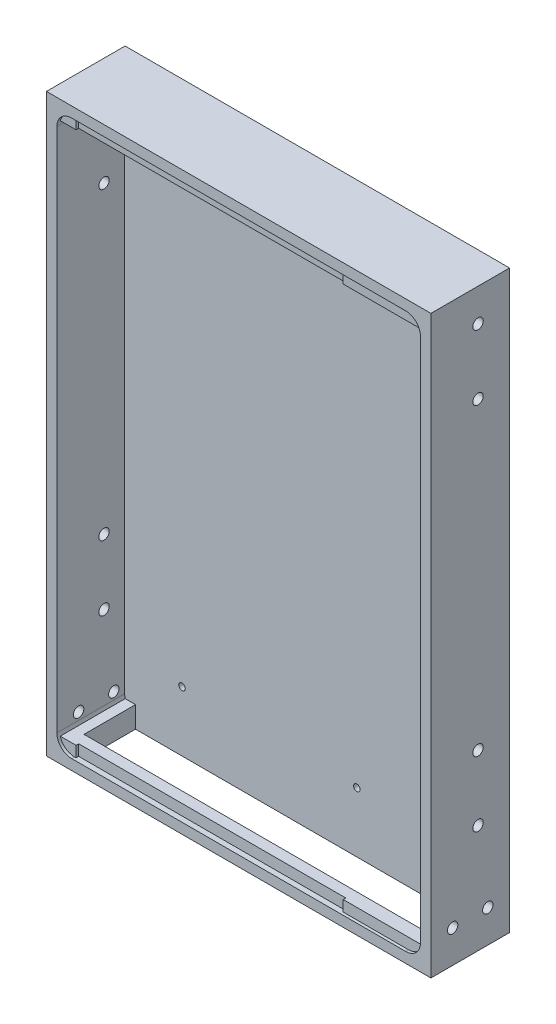
SolidWorks part; units mm, degrees
ref_plane "Front Plane" through (0, 0, 0) normal (0, 0, 1) x (1, 0, 0)
ref_plane "Top Plane" through (0, 0, 0) normal (0, 1, 0) x (1, 0, 0)
ref_plane "Right Plane" through (0, 0, 0) normal (1, 0, 0) x (0, 0, -1)
sketch "Sketch1" plane through (0, 0, 0) normal (0, 0, 1) x (1, 0, 0)
  line L1 (-88.5, -132.5) -> (88.5, -132.5)
  line L2 (-88.5, -132.5) -> (-88.5, 132.5)
  line L3 (-88.5, 132.5) -> (88.5, 132.5)
  line L4 (88.5, -132.5) -> (88.5, 132.5)
  line L5 (-88.5, -132.5) -> (88.5, 132.5) construction
  line L6 (-88.5, 132.5) -> (88.5, -132.5) construction
  circle A0 centre (-57.3, -104.9) radius 1.5 construction
  circle A1 centre (23.21, -104.9) radius 1.5 construction
  circle A2 centre (23.21, 104.9) radius 1.5 construction
  circle A3 centre (-57.3, 104.9) radius 1.5 construction
  circle A4 centre (-57.3, -104.9) radius 1.5
  circle A5 centre (23.21, -104.9) radius 1.5
  circle A6 centre (23.21, 104.9) radius 1.5
  circle A7 centre (-57.3, 104.9) radius 1.5
  point P0 (0, 0)
  dimension "D1" = 177
  dimension "D2" = 265
extrude "Boss-Extrude1" add sketch "Sketch1" along normal blind 5
sketch "Sketch2" plane through (0, 0, 5) normal (0, 0, 1) x (1, 0, 0)
  line L0 (83.7, -127.7) -> (83.7, 127.7)
  line L1 (83.7, 127.7) -> (-83.7, 127.7)
  line L2 (-83.7, 127.7) -> (-83.7, -127.7)
  line L3 (-83.7, -127.7) -> (83.7, -127.7)
  line L4 (88.5, -132.5) -> (88.5, 132.5)
  line L5 (88.5, 132.5) -> (-88.5, 132.5)
  line L6 (-88.5, 132.5) -> (-88.5, -132.5)
  line L7 (-88.5, -132.5) -> (88.5, -132.5)
  line L8 (88.5, -132.5) -> (88.5, 132.5)
  line L9 (88.5, 132.5) -> (-88.5, 132.5)
  line L10 (-88.5, 132.5) -> (-88.5, -132.5)
  line L11 (-88.5, -132.5) -> (88.5, -132.5)
  dimension "D1" = 0
  dimension "D2" = 4.8
extrude "Boss-Extrude2" add sketch "Sketch2" along normal blind 31.2
fillet "Fillet1" radius 6.82 4 edges at (83.7, 127.7, 20.6) (83.7, -127.7, 20.6) (-83.7, -127.7, 20.6) (-83.7, 127.7, 20.6)
sketch "Sketch4" plane through (0, 0, 5) normal (0, 0, 1) x (1, 0, 0)
  line L0 (-83.7, 122.7) -> (83.7, 122.7)
  line L1 (-83.7, -122.7) -> (83.7, -122.7)
  line L4 (83.7, -120.88) -> (83.7, 120.88)
  line L5 (76.88, 127.7) -> (-76.88, 127.7)
  line L6 (-83.7, 120.88) -> (-83.7, -120.88)
  line L7 (-76.88, -127.7) -> (76.88, -127.7)
  line L8 (83.7, -120.88) -> (83.7, 120.88)
  line L9 (76.88, 127.7) -> (-76.88, 127.7)
  line L10 (-83.7, 120.88) -> (-83.7, -120.88)
  line L11 (-76.88, -127.7) -> (76.88, -127.7)
  arc A4 (83.7, 120.88) -> (76.88, 127.7) centre (76.88, 120.88) ccw
  arc A5 (-76.88, 127.7) -> (-83.7, 120.88) centre (-76.88, 120.88) ccw
  arc A6 (-83.7, -120.88) -> (-76.88, -127.7) centre (-76.88, -120.88) ccw
  arc A7 (76.88, -127.7) -> (83.7, -120.88) centre (76.88, -120.88) ccw
  arc A8 (83.7, 120.88) -> (76.88, 127.7) centre (76.88, 120.88) ccw
  arc A9 (-76.88, 127.7) -> (-83.7, 120.88) centre (-76.88, 120.88) ccw
  arc A10 (-83.7, -120.88) -> (-76.88, -127.7) centre (-76.88, -120.88) ccw
  arc A11 (76.88, -127.7) -> (83.7, -120.88) centre (76.88, -120.88) ccw
  arc M12 (83.7, 120.88) -> (76.88, 127.7) centre (76.88, 120.88) ccw
  line M13 (76.88, 127.7) -> (-76.88, 127.7)
  arc M14 (-76.88, 127.7) -> (-83.7, 120.88) centre (-76.88, 120.88) ccw
  arc M16 (-83.7, -120.88) -> (-76.88, -127.7) centre (-76.88, -120.88) ccw
  line M17 (-76.88, -127.7) -> (76.88, -127.7)
  arc M18 (76.88, -127.7) -> (83.7, -120.88) centre (76.88, -120.88) ccw
  dimension "D2" = 5
  dimension "D3" = 5
  dimension "D1" = 0
extrude "Boss-Extrude3" add sketch "Sketch4" along normal offset from surface (29.9 mm away) 1.3 contours L1 M16 M17 M18 | L0 M14 M12 M13 up to face at (0, 0, 36.2)
sketch "Sketch5" plane through (0, 0, 34.9) normal (0, 0, 1) x (1, 0, 0)
  line L0 (83.4527, -122.7) -> (-83.4527, -122.7) construction
  line L1 (-76.88, -127.7) -> (76.88, -127.7) construction
  line L2 (76.88, 127.7) -> (-76.88, 127.7) construction
  line L3 (-83.4527, 122.7) -> (83.4527, 122.7) construction
  line L4 (83.4527, -122.7) -> (-83.4527, -122.7)
  line L5 (-76.88, -127.7) -> (76.88, -127.7)
  line L6 (76.88, 127.7) -> (-76.88, 127.7)
  line L7 (-83.4527, 122.7) -> (83.4527, 122.7)
  line L9 (-76.16, 127.7) -> (46.84, 127.7)
  line L10 (-76.16, 127.7) -> (-76.16, -127.7)
  line L11 (-76.16, -127.7) -> (46.84, -127.7)
  line L12 (46.84, 127.7) -> (46.84, -127.7)
  line L13 (-83.7, 120.88) -> (-83.7, -120.88) construction
  arc A0 (-83.4527, -122.7) -> (-76.88, -127.7) centre (-76.88, -120.88) ccw construction
  arc A1 (76.88, -127.7) -> (83.4527, -122.7) centre (76.88, -120.88) ccw construction
  arc A2 (-76.88, 127.7) -> (-83.4527, 122.7) centre (-76.88, 120.88) ccw construction
  arc A3 (83.4527, 122.7) -> (76.88, 127.7) centre (76.88, 120.88) ccw construction
  arc A4 (-83.4527, -122.7) -> (-76.88, -127.7) centre (-76.88, -120.88) ccw
  arc A5 (76.88, -127.7) -> (83.4527, -122.7) centre (76.88, -120.88) ccw
  arc A6 (-76.88, 127.7) -> (-83.4527, 122.7) centre (-76.88, 120.88) ccw
  arc A7 (83.4527, 122.7) -> (76.88, 127.7) centre (76.88, 120.88) ccw
  dimension "D1" = 7.54
  dimension "D2" = 123
extrude "Cut-Extrude1" cut sketch "Sketch5" against normal blind 1.2 contours L12 L4 L10 L5 | L12 L6 L10 L7
sketch "Sketch9" plane through (0, -122.7, 0) normal (0, 1, 0) x (1, 0, 0)
  line L0 (-83.4527, -5) -> (83.4527, -5) construction
  line L1 (-78.7, -5) -> (78.7, -5)
  line L2 (-78.7, -5) -> (-78.7, -28.7)
  line L3 (-78.7, -28.7) -> (78.7, -28.7)
  line L4 (78.7, -5) -> (78.7, -28.7)
  line L5 (-83.7, -36.2) -> (-83.7, -5) construction
  line L6 (46.84, -33.7) -> (-76.16, -33.7) construction
  line L7 (83.7, -5) -> (83.7, -36.2) construction
  dimension "D1" = 5
  dimension "D2" = 5
  dimension "D3" = 5
extrude "Cut-Extrude3" cut sketch "Sketch9" against normal through all
sketch "Sketch10" plane through (88.5, 0, 0) normal (1, 0, 0) x (0, 0, -1)
  circle A0 centre (-10, -117.5) radius 2.4 construction
  circle A1 centre (-26.2, -117.5) radius 2.4 construction
  circle A2 centre (-10, -117.5) radius 2.4
  circle A3 centre (-26.2, -117.5) radius 2.4
extrude "Cut-Extrude4" cut sketch "Sketch10" against normal through all
sketch "Sketch11" plane through (0, 0, 0) normal (0, 0, -1) x (-1, 0, 0)
  line L0 (88.5, 132.5) -> (108.5, 132.5)
  line L1 (108.5, 132.5) -> (108.5, 82.5)
  line L2 (108.5, 82.5) -> (88.5, 82.5)
  line L3 (88.5, 132.5) -> (88.5, -132.5) construction
  line L4 (88.5, 82.5) -> (88.5, 132.5)
  line L9 (0, 132.5) -> (0, 0) construction
  line L10 (-88.5, 132.5) -> (88.5, 132.5) construction
  dimension "D1" = 50
  dimension "D2" = 20
sketch "Sketch16" plane through (88.5, 0, 0) normal (1, 0, 0) x (0, 0, -1)
  line L0 (0, -132.5) -> (0, 132.5) construction
  line L1 (-36.2, 132.5) -> (0, 132.5) construction
  line L2 (-14.5, 117.5) -> (-14.5, 87.5) construction
  line L3 (-14.5, 87.5) -> (-14.5, -52.5) construction
  line L4 (-14.5, -52.5) -> (-14.5, -82.5) construction
  line L8 (-36.2, 120.88) -> (-36.2, -120.88)
  line L9 (-36.2, -120.88) -> (-5, -120.88)
  line L10 (-5, -120.88) -> (-5, 120.88)
  line L11 (-5, 120.88) -> (-36.2, 120.88)
  line L16 (-36.2, 120.88) -> (-36.2, -120.88) construction
  line L17 (-36.2, -120.88) -> (-5, -120.88) construction
  line L18 (-5, -120.88) -> (-5, 120.88) construction
  line L19 (-5, 120.88) -> (-36.2, 120.88) construction
  circle A1 centre (-14.5, 117.5) radius 2.4
  circle A2 centre (-14.5, 87.5) radius 2.4
  circle A3 centre (-14.5, -52.5) radius 2.4
  circle A4 centre (-14.5, -82.5) radius 2.4
  dimension "D3" = 4.8
  dimension "D2" = 14.5
  dimension "D4" = 15
  dimension "D5" = 30
  dimension "D6" = 140
  dimension "D1" = 0
extrude "Cut-Extrude7" cut sketch "Sketch16" against normal up to surface (177 mm away) up to face at (-88.5, -117.5, 7.6)
